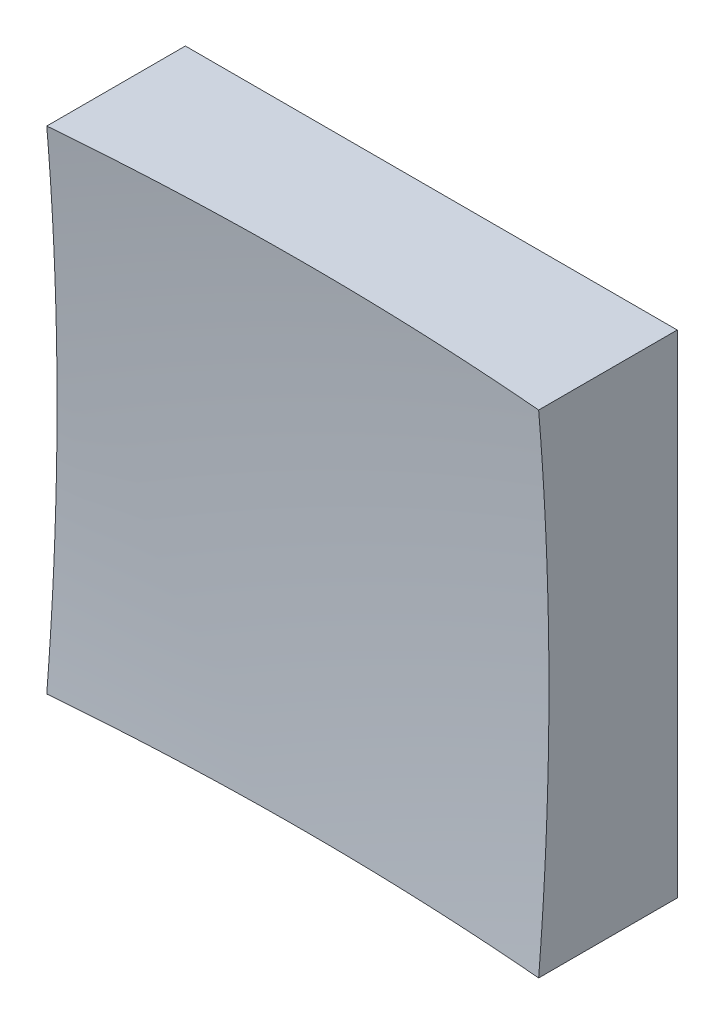
SolidWorks part; units mm, degrees
ref_plane "前视基准面" through (0, 0, 0) normal (0, 0, 1) x (1, 0, 0)
ref_plane "上视基准面" through (0, 0, 0) normal (0, 1, 0) x (1, 0, 0)
ref_plane "右视基准面" through (0, 0, 0) normal (1, 0, 0) x (0, 0, -1)
sketch "草图1" plane through (0, 0, 0) normal (0, 0, 1) x (1, 0, 0)
  line L1 (-12.5, 12.5) -> (12.5, 12.5)
  line L2 (-12.5, 12.5) -> (-12.5, -12.5)
  line L3 (-12.5, -12.5) -> (12.5, -12.5)
  line L4 (12.5, 12.5) -> (12.5, -12.5)
  line L5 (-12.5, 12.5) -> (12.5, -12.5) construction
  line L6 (-12.5, -12.5) -> (12.5, 12.5) construction
  point P0 (0, 0)
  dimension "D1" = 25
  dimension "D2" = 25
extrude "凸台-拉伸1" add sketch "草图1" along normal blind 20 contours L2 L3 L4 L1
sketch "草图2" plane through (0, 0, 0) normal (0, 1, 0) x (1, 0, 0)
  line L0 (-7.4603, -6) -> (7.3192, -6) construction
  line L1 (0, 0) -> (0, -12.1749) construction
  line L2 (146.2268, -122.5677) -> (0, -122.5677)
  line L3 (0, -122.5677) -> (0, -6)
  arc A1 (146.2268, -122.5677) -> (0, -6) centre (0, -156) ccw
  dimension "D2" = 300
  dimension "D1" = 6
revolve "切除-旋转2" cut sketch "草图2" angle 360 about L3
